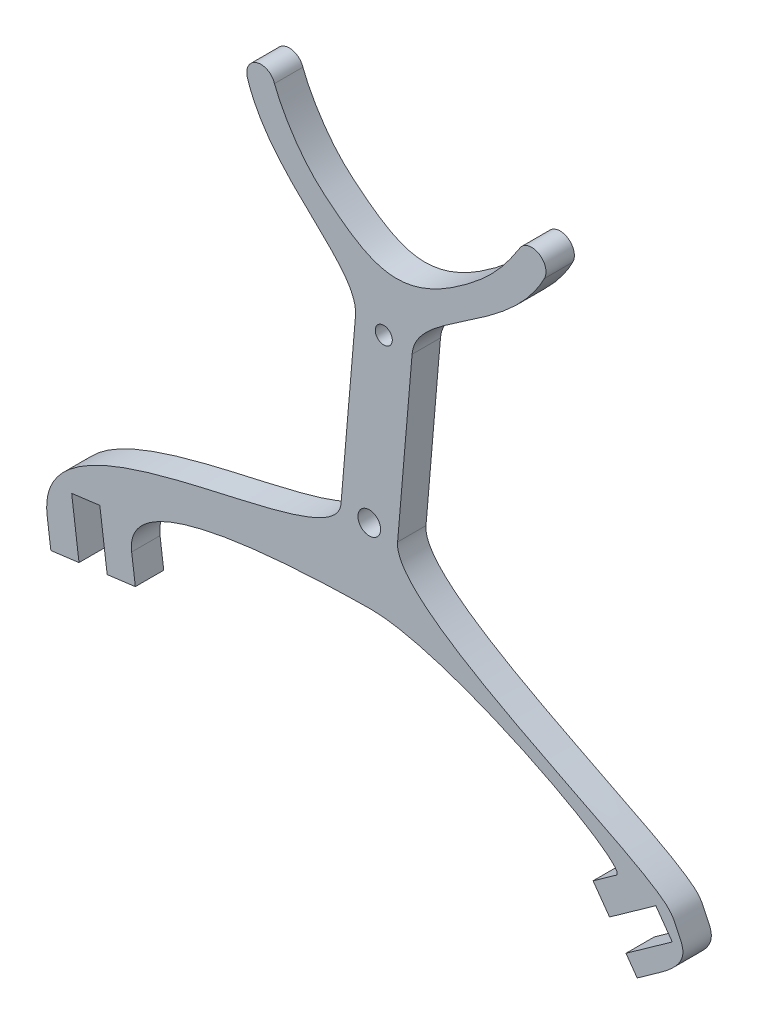
SolidWorks part; units mm, degrees
ref_plane "Alzado" through (0, 0, 0) normal (0, 0, 1) x (1, 0, 0)
ref_plane "Planta" through (0, 0, 0) normal (0, 1, 0) x (1, 0, 0)
ref_plane "Vista lateral" through (0, 0, 0) normal (1, 0, 0) x (0, 0, -1)
sketch "Croquis2" plane through (0, 0, 0) normal (0, 0, 1) x (1, 0, 0)
  line L1 (-0.0205, 0.0015) -> (0.2159, 2.773) construction
  line L3 (-0.2696, 0.0228) -> (-0.1421, 1.5174)
  line L4 (0.2286, -0.0197) -> (0.3561, 1.4749)
  line L5 (-0.0268, 2.8696) -> (-0.0255, 2.8844)
  line L7 (-0.2696, 0.0228) -> (0.2286, -0.0197) construction
  line L54 (0, 3.5) -> (1.2986, 2.7493) construction
  line L56 (1.2986, 2.7493) -> (1.5206, 2.6344) construction
  line L58 (-2.5759, -1.5791) -> (-2.6404, -1.0833)
  line L59 (2.094, -1.946) -> (2.5015, -1.6563)
  line L61 (2.5015, -1.6563) -> (2.6464, -1.86)
  line L63 (2.6464, -1.86) -> (2.2389, -2.1498)
  line L64 (2.094, -1.946) -> (1.9492, -1.7423)
  line L66 (-2.6404, -1.0833) -> (-2.3925, -1.051)
  line L67 (-2.3925, -1.051) -> (-2.3279, -1.5468)
  line L68 (-2.3279, -1.5468) -> (-2.08, -1.5146)
  line L69 (-2.5759, -1.5791) -> (-2.8238, -1.6114)
  line L70 (-2.8238, -1.6114) -> (-2.856, -1.3635)
  line L71 (-2.08, -1.5146) -> (-2.1123, -1.2667)
  line L73 (2.3379, -2.289) -> (2.5416, -2.1441)
  line L74 (2.2389, -2.1498) -> (2.3379, -2.289)
  line L77 (1.9492, -1.7423) -> (2.1529, -1.5974)
  circle A3 centre (0, 3.5) radius 1.5 construction
  circle A6 centre (0, 3.5) radius 0.5 construction
  circle A7 centre (-0.0205, 0.0015) radius 0.1
  arc A8 (0.5139, 2.0908) -> (1.2986, 2.7493) centre (0, 3.5) ccw construction
  arc A9 (1.2986, 2.7493) -> (1.5206, 2.6344) centre (1.4096, 2.6919) cw
  arc A10 (-0.8551, 2.933) -> (-1.0934, 2.8574) centre (-0.9743, 2.8952) ccw
  arc A11 (-0.0074, 2.0611) -> (-0.8551, 2.933) centre (0.5518, 3.4529) cw construction
  spline S0 degree 3 poles (0.3561, 1.4749) (0.3884, 1.8531) (1.2055, 2.0256) (1.5206, 2.6344) knots 0 0 0 0 1 1 1 1
  spline S1 degree 3 poles (-0.1421, 1.5174) (-0.1098, 1.8956) (-0.8859, 2.204) (-1.0934, 2.8574) knots 0 0 0 0 1 1 1 1
  spline S2 degree 3 poles (0.2286, -0.0197) (0.186, -0.5188) (2.5752, -1.4152) (2.7032, -1.8133) (2.8298, -1.9392) (2.5416, -2.1441) knots 0 0 0 0 0.59818 0.69818 1 1 1 1
  spline S3 degree 3 poles (-0.2696, 0.0228) (-0.3136, -0.493) (-2.983, -0.3876) (-2.856, -1.3635) knots 0 0 0 0 1 1 1 1
  spline S4 degree 2 poles (-2.1123, -1.2667) (-2.1889, -0.6779) (0, -0.6493) knots 0 0 0 1 1 1
  spline S5 degree 3 poles (0, -0.6493) (0.7337, -0.6581) (2.2931, -1.4977) (2.1529, -1.5974) knots 0 0 0 0 1 1 1 1
  spline S6 degree 3 poles (-0.8551, 2.933) (-0.8029, 2.7915) (-0.6268, 2.4783) (-0.0356, 1.9918) (0.3017, 1.8375) (1.0442, 2.406) (1.1894, 2.58) (1.2986, 2.7493) knots 0 0 0 0 0.244258 0.3308 0.806015 0.878875 1 1 1 1
  point P3 (0, 3.5)
  point P20 (-0.0205, 0.0015)
  point P150 (0, -0.3421)
  point P156 (0.3032, 2.031)
  point P159 (0.0042, 2.0565)
  dimension "D1" = 0.2
  dimension "D4" = 1.5
  dimension "D8" = 0.25
  dimension "D11" = 0.25
  dimension "D13" = 0.5
  dimension "D17" = 0.25
  dimension "D19" = 0.25
  dimension "D3" = 0.25
  dimension "D9" = 0.5
  dimension "D10" = 0.25
  dimension "D12" = 0.25
  dimension "D14" = 0.25
  dimension "D15" = 0.25
  dimension "D16" = 0.25
  dimension "D21" = 0.25
extrude "Saliente-Extruir1" add sketch "Croquis2" along normal blind 0.25
sketch "Croquis3" plane through (0, 0, 0.25) normal (0, 0, 1) x (1, 0, 0)
  line L1 (-0.2696, 0.0228) -> (-0.1421, 1.5174) construction
  circle A0 centre (0.107, 1.4962) radius 0.075
  dimension "D1" = 0.15
  dimension "D2" = 1.5
  dimension "D3" = 0.25
extrude "Cortar-Extruir1" cut sketch "Croquis3" against normal up to next
